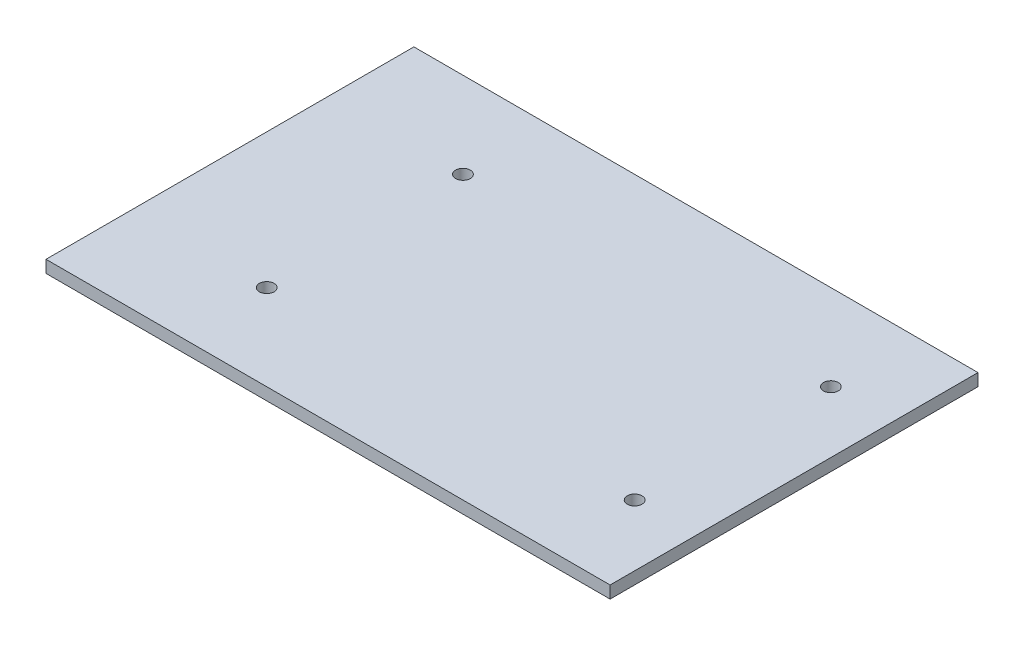
SolidWorks part; units mm, degrees
ref_plane "Front Plane" through (0, 0, 0) normal (0, 0, 1) x (1, 0, 0)
ref_plane "Top Plane" through (0, 0, 0) normal (0, 1, 0) x (1, 0, 0)
ref_plane "Right Plane" through (0, 0, 0) normal (1, 0, 0) x (0, 0, -1)
sketch "Sketch1" plane through (0, 0, 0) normal (0, 1, 0) x (1, 0, 0)
  line L1 (0, 0) -> (230, 0)
  line L2 (0, 0) -> (0, 150)
  line L3 (0, 150) -> (230, 150)
  line L4 (230, 0) -> (230, 150)
  dimension "D1" = 230
  dimension "D2" = 150
extrude "Boss-Extrude1" add sketch "Sketch1" along normal blind 5
sketch "Sketch2" plane through (0, 5, 0) normal (0, 1, 0) x (1, 0, 0)
  line L0 (230, 150) -> (0, 150) construction
  line L1 (0, 0) -> (230, 0) construction
  line L2 (0, 150) -> (0, 0) construction
  circle A0 centre (7.5, 125) radius 1.25
  circle A1 centre (7.5, 25) radius 1.25
  dimension "D1" = 2.5
  dimension "D2" = 2.5
  dimension "D3" = 25
  dimension "D4" = 25
  dimension "D5" = 7.5
  dimension "D6" = 7.5
extrude "Cut-Extrude1" [suppressed] cut sketch "Sketch2" against normal through all
ref_plane "Plane1" through (115, 0, 0) normal (-1, 0, 0) x (0, 0, 1)
mirror "Mirror1" [suppressed] about plane through (115, 0, 0) normal (-1, 0, 0)
sketch "Sketch3" plane through (0, 5, 0) normal (0, 1, 0) x (1, 0, 0)
  line L0 (0, 0) -> (230, 0) construction
  line L1 (230, 0) -> (230, 150) construction
  line L2 (230, 150) -> (0, 150) construction
  circle A0 centre (205, 35) radius 3
  circle A1 centre (205, 115) radius 3
  dimension "D2" = 6
  dimension "D4" = 6
  dimension "D1" = 35
  dimension "D3" = 25
  dimension "D5" = 35
  dimension "D6" = 25
extrude "Cut-Extrude2" cut sketch "Sketch3" against normal through all
sketch "Sketch4" plane through (0, 5, 0) normal (0, 1, 0) x (1, 0, 0)
  line L0 (0, 0) -> (230, 0) construction
  line L1 (0, 150) -> (0, 0) construction
  line L2 (230, 150) -> (0, 150) construction
  circle A0 centre (55, 115) radius 3
  circle A1 centre (55, 35) radius 3
  dimension "D1" = 6
  dimension "D2" = 6
  dimension "D3" = 35
  dimension "D4" = 55
  dimension "D5" = 35
  dimension "D6" = 55
extrude "Cut-Extrude3" cut sketch "Sketch4" against normal blind 10
